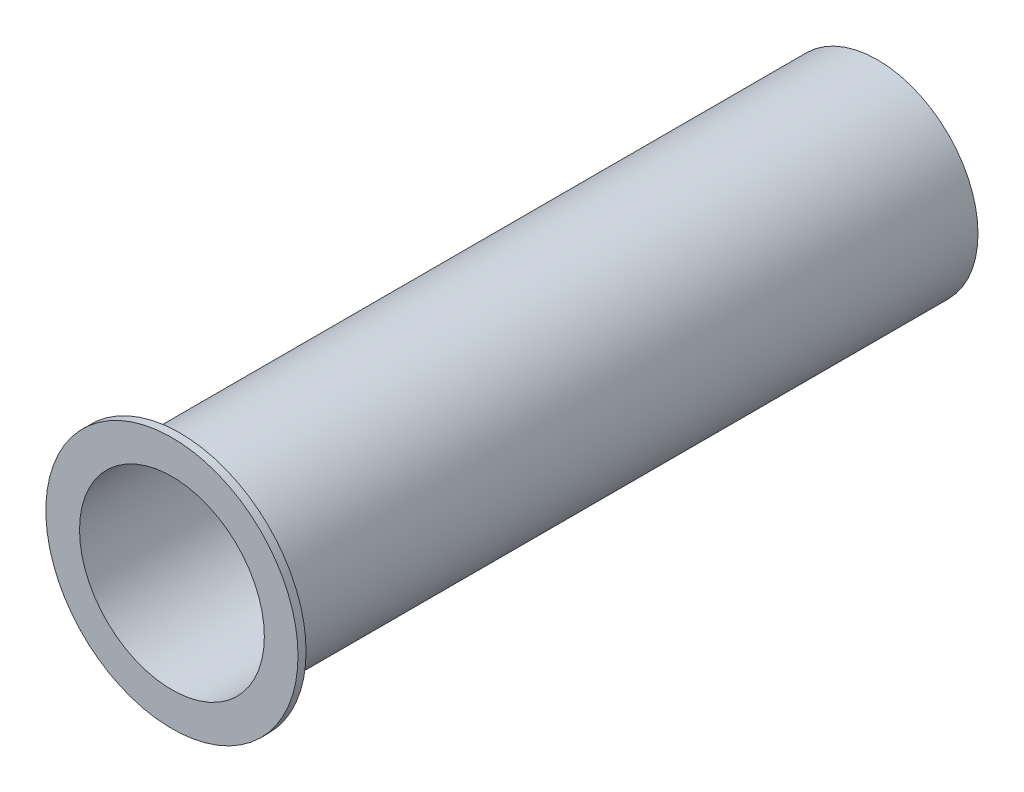
SolidWorks part; units mm, degrees
material "Laiton"
ref_plane "Plan de face" through (0, 0, 0) normal (0, 0, 1) x (1, 0, 0)
ref_plane "Plan de dessus" through (0, 0, 0) normal (0, 1, 0) x (1, 0, 0)
ref_plane "Plan de droite" through (0, 0, 0) normal (1, 0, 0) x (0, 0, -1)
sketch "Esquisse1" plane through (0, 0, 0) normal (0, 0, 1) x (1, 0, 0)
  circle A0 centre (0, 0) radius 6.25
  circle A1 centre (0, 0) radius 5.75
  dimension "D1" = 12.5
  dimension "D2" = 0.5
extrude "Boss.-Extru.1" add sketch "Esquisse1" along normal blind 43.4
sketch "Esquisse2" plane through (0, 0, 43.4) normal (0, 0, 1) x (1, 0, 0)
  circle A0 centre (0, 0) radius 7.845
  circle A1 centre (0, 0) radius 5.75
  dimension "D1" = 15.69
extrude "Boss.-Extru.2" add sketch "Esquisse2" along normal blind 0.5
